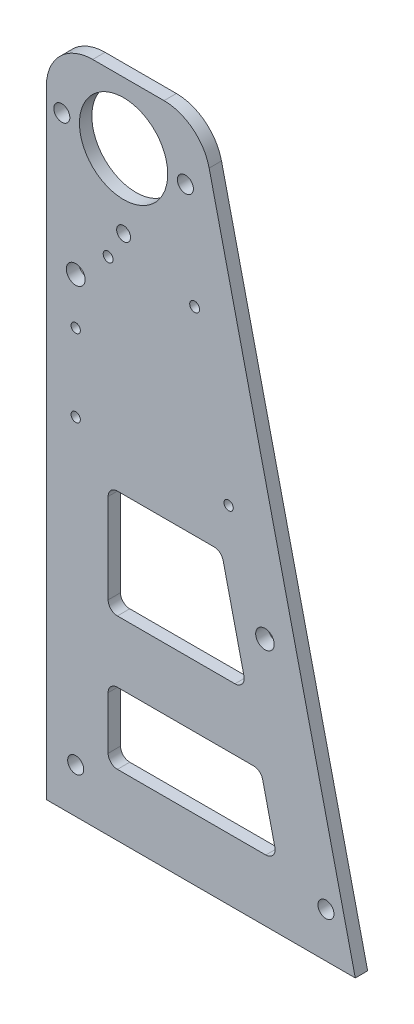
SolidWorks part; units mm, degrees
material "Gerais  - 6061-T6"
ref_plane "Plano frontal" through (0, 0, 0) normal (0, 0, 1) x (1, 0, 0)
ref_plane "Plano superior" through (0, 0, 0) normal (0, 1, 0) x (1, 0, 0)
ref_plane "Plano direito" through (0, 0, 0) normal (1, 0, 0) x (0, 0, -1)
sketch "Esboço1" plane through (0, 0, 0) normal (0, 0, 1) x (1, 0, 0)
  line L0 (0, 0) -> (0, 215)
  line L2 (100, 0) -> (0, 0)
  line L3 (0, 215) -> (50, 215)
  line L4 (50, 215) -> (100, 0)
  line L5 (10, 103) -> (10, 15) construction
  line L6 (25, 215) -> (25, 175) construction
  line L7 (10, 15) -> (75.7552, 15) construction
  line L8 (75.7552, 15) -> (55.2901, 103) construction
  line L9 (55.2901, 103) -> (10, 103) construction
  line L10 (20, 95) -> (20, 66)
  line L11 (23, 63) -> (61.0374, 63)
  line L12 (63.9594, 66.6795) -> (57.2152, 95.6795)
  line L13 (54.2932, 98) -> (23, 98)
  line L14 (20, 40) -> (20, 23)
  line L15 (23, 20) -> (71.0374, 20)
  line L16 (73.9594, 23.6795) -> (70.0059, 40.6795)
  line L17 (23, 43) -> (67.0839, 43)
  line L18 (0, 195) -> (50, 195) construction
  line L23 (17, 205) -> (33, 185) construction
  line L24 (17, 185) -> (33, 205) construction
  arc A8 (70.0059, 40.6795) -> (67.0839, 43) centre (67.0839, 40) ccw
  arc A9 (71.0374, 20) -> (73.9594, 23.6795) centre (71.0374, 23) ccw
  arc A10 (20, 23) -> (23, 20) centre (23, 23) ccw
  arc A11 (20, 40) -> (23, 43) centre (23, 40) cw
  arc A12 (57.2152, 95.6795) -> (54.2932, 98) centre (54.2932, 95) ccw
  arc A13 (61.0374, 63) -> (63.9594, 66.6795) centre (61.0374, 66) ccw
  arc A14 (20, 66) -> (23, 63) centre (23, 66) ccw
  arc A15 (20, 95) -> (23, 98) centre (23, 95) cw
  circle A20 centre (25, 195) radius 14.2875
  circle A21 centre (9.5, 14.5) radius 2.6
  point P8 (25, 195)
  point P49 (20, 63)
  dimension "D3" = 20
  dimension "D4" = 16
  dimension "D7" = 28.575
  dimension "D21" = 3
  dimension "D20" = 9.5
  dimension "D22" = 5.2
  dimension "D1" = 215
  dimension "D2" = 100
  dimension "D5" = 50
  dimension "D9" = 20
  dimension "D10" = 20
  dimension "D11" = 10
  dimension "D12" = 20
  dimension "D13" = 15
  dimension "D14" = 20
  dimension "D15" = 10
  dimension "D16" = 29
  dimension "D17" = 17
  dimension "D18" = 10
  dimension "D19" = 14.5
  dimension "D8" = 20
extrude "Ressalto-extrusão2" add sketch "Esboço1" along normal blind 4
fillet "Filete1" radius 15 2 edges at (0, 215, 2) (50, 215, 2)
sketch "Esboço3" plane through (0, 0, 0) normal (0, 0, -1) x (-1, 0, 0)
  line L1 (0, 0) -> (-100, 0) construction
  line L2 (0, 200) -> (0, 0) construction
  circle A0 centre (-9.5, 112) radius 1.5
  circle A1 centre (-90.5, 14.5) radius 2.6
  circle A2 centre (-9.5, 137) radius 1.5
  circle A3 centre (-9.5, 152) radius 3.05
  circle A4 centre (-59, 112) radius 1.5
  point P6 (-9.5, 112)
  point P9 (-9.5, 137)
  dimension "D5" = 5.2
  dimension "D1" = 25
  dimension "D6" = 3
  dimension "D7" = 112
  dimension "D8" = 15
  dimension "D9" = 6.1
  dimension "D10" = 49.5
  dimension "D2" = 9.5
  dimension "D3" = 14.5
  dimension "D4" = 9.5
extrude "Corte-extrusão1" cut sketch "Esboço3" against normal through all
sketch "Esboço5" plane through (0, 0, 0) normal (0, 0, -1) x (-1, 0, 0)
  line L0 (-45, 195) -> (-5, 195) construction
  circle A0 centre (-25, 171.1875) radius 2.25
  circle A1 centre (-70.7598, 80.3986) radius 3
  circle A2 centre (-25, 195) radius 14.2875 construction
  circle A3 centre (-20, 162.1875) radius 1.6
  circle A4 centre (-48, 162.1875) radius 1.6
  circle A5 centre (-45, 195) radius 2.6
  circle A6 centre (-5, 195) radius 2.6
  point P6 (-25, 195)
  point P17 (-2.4, 195)
  dimension "D1" = 23.8125
  dimension "D2" = 4.5
  dimension "D4" = 28
  dimension "D6" = 3.2
  dimension "D7" = 40
  dimension "D8" = 5.2
  dimension "D3" = 5
  dimension "D5" = 9
extrude "Corte-extrusão2" cut sketch "Esboço5" against normal through all
